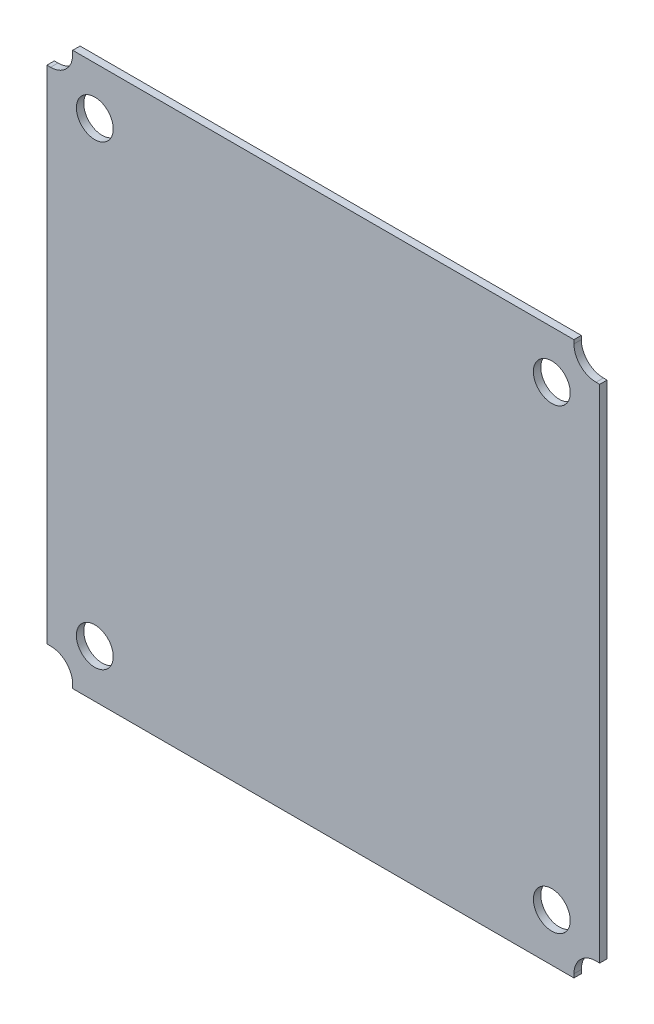
SolidWorks part; units mm, degrees
ref_plane "正面" through (0, 0, 0) normal (0, 0, 1) x (1, 0, 0)
ref_plane "平面" through (0, 0, 0) normal (0, 1, 0) x (1, 0, 0)
ref_plane "右側面" through (0, 0, 0) normal (1, 0, 0) x (0, 0, -1)
sketch "ｽｹｯﾁ1" plane through (0, 0, 0) normal (0, 0, 1) x (1, 0, 0)
  line L1 (-45, 45) -> (45, 45)
  line L2 (-45, 45) -> (-45, -45)
  line L3 (-45, -45) -> (45, -45)
  line L4 (45, 45) -> (45, -45)
  line L5 (-45, 34) -> (45, 34)
  line L6 (-45, 34) -> (-45, -34)
  line L7 (-45, -34) -> (45, -34)
  line L8 (45, 34) -> (45, -34)
  line L9 (-34, 45) -> (34, 45)
  line L10 (-34, 45) -> (-34, -45)
  line L11 (-34, -45) -> (34, -45)
  line L12 (34, 45) -> (34, -45)
  circle A0 centre (-31, 31) radius 2.5
  circle A1 centre (31, 31) radius 2.5
  circle A2 centre (31, -31) radius 2.5
  circle A3 centre (-31, -31) radius 2.5
  dimension "D15" = 5
  dimension "D16" = 5
  dimension "D17" = 5
  dimension "D18" = 5
  dimension "D1" = 90
  dimension "D2" = 90
  dimension "D3" = 45
  dimension "D4" = 45
  dimension "D5" = 68
  dimension "D6" = 34
  dimension "D7" = 68
  dimension "D8" = 34
  dimension "D9" = 62
  dimension "D10" = 62
  dimension "D11" = 62
  dimension "D12" = 62
  dimension "D13" = 31
  dimension "D14" = 31
extrude "ﾎﾞｽ - 押し出し2" add sketch "ｽｹｯﾁ1" along normal blind 1 contours L12 L5 L10 L7 A3 A2 A1 A0 | L12 L1 L10 L5 | L10 L5 L2 L7 | L5 L12 L7 L4 | L12 L7 L10 L3
fillet "ﾌｨﾚｯﾄ1" radius 3 4 edges at (34, -34, 0.5) (-34, -34, 0.5) (34, 34, 0.5) (-34, 34, 0.5)
sketch "ｽｹｯﾁ2" plane through (0, 0, 1) normal (0, 0, 1) x (1, 0, 0)
  line L0 (34, 45) -> (34, 37) construction
  line L1 (-37.5, 37.5) -> (37.5, 37.5)
  line L2 (-37.5, 37.5) -> (-37.5, -37.5)
  line L3 (-37.5, -37.5) -> (37.5, -37.5)
  line L4 (37.5, 37.5) -> (37.5, -37.5)
  line L5 (-34, 45) -> (34, 45)
  line L6 (-34, 45) -> (-34, 37.5)
  line L7 (-34, 37.5) -> (34, 37.5)
  line L8 (34, 45) -> (34, 37.5)
  line L9 (-45, -34) -> (-37, -34) construction
  line L10 (-45, 34) -> (-37.5, 34)
  line L11 (-45, 34) -> (-45, -34)
  line L12 (-45, -34) -> (-37.5, -34)
  line L13 (-37.5, 34) -> (-37.5, -34)
  line L14 (34, -37) -> (34, -45) construction
  line L15 (-34, -45) -> (34, -45)
  line L16 (-34, -45) -> (-34, -37.5)
  line L17 (-34, -37.5) -> (34, -37.5)
  line L18 (34, -45) -> (34, -37.5)
  line L20 (45, -34) -> (37.5, -34)
  line L21 (45, -34) -> (45, 34)
  line L22 (45, 34) -> (37.5, 34)
  line L23 (37.5, -34) -> (37.5, 34)
  line M7 (34, -45) -> (34, -37)
  line M9 (37, -34) -> (45, -34)
  line M10 (45, -34) -> (45, 34)
  line M11 (45, 34) -> (37, 34)
  line M13 (34, 37) -> (34, 45)
  line M14 (34, 45) -> (-34, 45)
  line M15 (-34, 45) -> (-34, 37)
  line M17 (-37, 34) -> (-45, 34)
  line M18 (-45, 34) -> (-45, -34)
  line M19 (-45, -34) -> (-37, -34)
  line M21 (-34, -37) -> (-34, -45)
  line M22 (-34, -45) -> (34, -45)
  dimension "D1" = 75
  dimension "D2" = 75
  dimension "D3" = 37.5
  dimension "D4" = 37.5
extrude "ｶｯﾄ - 押し出し1" cut sketch "ｽｹｯﾁ2" against normal through all contours L2 M17 M18 M19 | L1 M15 M13 M14 | L4 M11 M9 M10 | L3 M21 M22 M7
